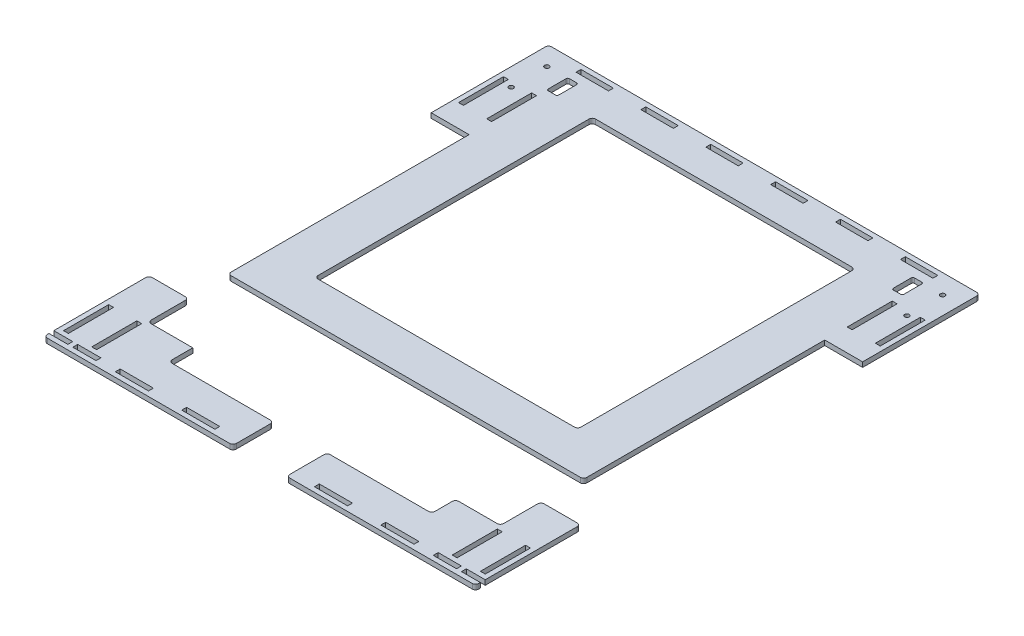
SolidWorks part; units mm, degrees
ref_plane "Front Plane" through (0, 0, 0) normal (0, 0, 1) x (1, 0, 0)
ref_plane "Top Plane" through (0, 0, 0) normal (0, 1, 0) x (1, 0, 0)
ref_plane "Right Plane" through (0, 0, 0) normal (1, 0, 0) x (0, 0, -1)
sketch "Sketch1" plane through (0, 0, 0) normal (0, 1, 0) x (1, 0, 0)
  line L0 (-127, 149.5) -> (-127, 155.5) construction
  line L1 (-133, -155.5) -> (133, -155.5)
  line L2 (-133, -155.5) -> (-133, 155.5)
  line L3 (-133, 155.5) -> (133, 155.5)
  line L4 (133, -155.5) -> (133, 155.5)
  line L5 (-133, -155.5) -> (133, 155.5) construction
  line L6 (-133, 155.5) -> (133, -155.5) construction
  line L7 (-130, -152.5) -> (130, -152.5) construction
  line L8 (-130, -152.5) -> (-130, 152.5) construction
  line L9 (-130, 152.5) -> (130, 152.5) construction
  line L10 (130, -152.5) -> (130, 152.5) construction
  line L11 (-130, -152.5) -> (130, 152.5) construction
  line L12 (-130, 152.5) -> (130, -152.5) construction
  line L13 (-127, -149.5) -> (127, -149.5) construction
  line L14 (-127, -149.5) -> (-127, 149.5) construction
  line L15 (-127, 149.5) -> (127, 149.5) construction
  line L16 (127, -149.5) -> (127, 149.5) construction
  line L17 (-127, -149.5) -> (127, 149.5) construction
  line L18 (-127, 149.5) -> (127, -149.5) construction
  line L19 (-127, 149.5) -> (-133, 149.5) construction
  line L20 (-130, 152.5) -> (-110, 152.5) construction
  line L21 (-110, 149.5) -> (-90, 149.5)
  line L22 (-110, 149.5) -> (-110, 152.5)
  line L23 (-110, 152.5) -> (-90, 152.5)
  line L24 (-90, 149.5) -> (-90, 152.5)
  line L25 (-110, 149.5) -> (-90, 152.5) construction
  line L26 (-110, 152.5) -> (-90, 149.5) construction
  line L27 (-30, 149.5) -> (-10, 149.5)
  line L28 (-30, 149.5) -> (-30, 152.5)
  line L29 (-30, 152.5) -> (-10, 152.5)
  line L30 (-10, 149.5) -> (-10, 152.5)
  line L31 (-30, 149.5) -> (-10, 152.5) construction
  line L32 (-30, 152.5) -> (-10, 149.5) construction
  line L33 (-70, 149.5) -> (-50, 149.5)
  line L34 (-70, 149.5) -> (-70, 152.5)
  line L35 (-70, 152.5) -> (-50, 152.5)
  line L36 (-50, 149.5) -> (-50, 152.5)
  line L37 (-70, 149.5) -> (-50, 152.5) construction
  line L38 (-70, 152.5) -> (-50, 149.5) construction
  line L39 (10, 149.5) -> (30, 149.5)
  line L40 (10, 149.5) -> (10, 152.5)
  line L41 (10, 152.5) -> (30, 152.5)
  line L42 (30, 149.5) -> (30, 152.5)
  line L43 (10, 149.5) -> (30, 152.5) construction
  line L44 (10, 152.5) -> (30, 149.5) construction
  line L45 (50, 149.5) -> (70, 149.5)
  line L46 (50, 149.5) -> (50, 152.5)
  line L47 (50, 152.5) -> (70, 152.5)
  line L48 (70, 149.5) -> (70, 152.5)
  line L49 (50, 149.5) -> (70, 152.5) construction
  line L50 (50, 152.5) -> (70, 149.5) construction
  line L51 (90, 149.5) -> (110, 149.5)
  line L52 (90, 149.5) -> (90, 152.5)
  line L53 (90, 152.5) -> (110, 152.5)
  line L54 (110, 149.5) -> (110, 152.5)
  line L55 (90, 149.5) -> (110, 152.5) construction
  line L56 (90, 152.5) -> (110, 149.5) construction
  line L57 (-90, 152.5) -> (-70, 152.5) construction
  line L58 (-50, 152.5) -> (-30, 152.5) construction
  line L59 (-10, 152.5) -> (10, 152.5) construction
  line L60 (30, 152.5) -> (50, 152.5) construction
  line L61 (70, 152.5) -> (90, 152.5) construction
  line L62 (110, 152.5) -> (130, 152.5) construction
  line L63 (10.2307, -149.5) -> (30.6922, -149.5) construction
  line L64 (-10.2308, -152.5) -> (10.2307, -152.5)
  line L65 (-10.2308, -152.5) -> (-10.2308, -149.5)
  line L66 (-10.2308, -149.5) -> (10.2307, -149.5)
  line L67 (10.2307, -152.5) -> (10.2307, -149.5)
  line L68 (-10.2308, -152.5) -> (10.2307, -149.5) construction
  line L69 (-10.2308, -149.5) -> (10.2307, -152.5) construction
  line L70 (30.6922, -152.5) -> (51.1537, -152.5)
  line L71 (30.6922, -152.5) -> (30.6922, -149.5)
  line L72 (30.6922, -149.5) -> (51.1537, -149.5)
  line L73 (51.1537, -152.5) -> (51.1537, -149.5)
  line L74 (30.6922, -152.5) -> (51.1537, -149.5) construction
  line L75 (30.6922, -149.5) -> (51.1537, -152.5) construction
  line L76 (92.0767, -152.5) -> (71.6152, -152.5)
  line L77 (92.0767, -152.5) -> (92.0767, -149.5)
  line L78 (92.0767, -149.5) -> (71.6152, -149.5)
  line L79 (71.6152, -152.5) -> (71.6152, -149.5)
  line L80 (92.0767, -152.5) -> (71.6152, -149.5) construction
  line L81 (92.0767, -149.5) -> (71.6152, -152.5) construction
  line L82 (-51.1538, -152.5) -> (-30.6923, -152.5)
  line L83 (-51.1538, -152.5) -> (-51.1538, -149.5)
  line L84 (-51.1538, -149.5) -> (-30.6923, -149.5)
  line L85 (-30.6923, -152.5) -> (-30.6923, -149.5)
  line L86 (-51.1538, -152.5) -> (-30.6923, -149.5) construction
  line L87 (-51.1538, -149.5) -> (-30.6923, -152.5) construction
  line L88 (-92.0768, -152.5) -> (-71.6153, -152.5)
  line L89 (-92.0768, -152.5) -> (-92.0768, -149.5)
  line L90 (-92.0768, -149.5) -> (-71.6153, -149.5)
  line L91 (-71.6153, -152.5) -> (-71.6153, -149.5)
  line L92 (-92.0768, -152.5) -> (-71.6153, -149.5) construction
  line L93 (-92.0768, -149.5) -> (-71.6153, -152.5) construction
  line L94 (51.1537, -149.5) -> (71.6152, -149.5) construction
  line L95 (-10.2308, -149.5) -> (-30.6923, -149.5) construction
  line L96 (-51.1538, -149.5) -> (-71.6153, -149.5) construction
  line L97 (-133, 83.1818) -> (-109.65, 83.1818)
  line L98 (133, -152.5) -> (103.975, -152.5)
  line L99 (133, -152.5) -> (133, -149.5)
  line L100 (133, -149.5) -> (103.975, -149.5)
  line L101 (103.975, -152.5) -> (103.975, -149.5)
  line L102 (133, -152.5) -> (103.975, -149.5) construction
  line L103 (133, -149.5) -> (103.975, -152.5) construction
  line L104 (-133, -152.5) -> (-103.975, -152.5)
  line L105 (-133, -152.5) -> (-133, -149.5)
  line L106 (-133, -149.5) -> (-103.975, -149.5)
  line L107 (-103.975, -152.5) -> (-103.975, -149.5)
  line L108 (-133, -152.5) -> (-103.975, -149.5) construction
  line L109 (-133, -149.5) -> (-103.975, -152.5) construction
  line L110 (127, -118.6591) -> (130, -118.6591)
  line L111 (127, -118.6591) -> (127, -146.5)
  line L112 (127, -146.5) -> (130, -146.5)
  line L113 (130, -118.6591) -> (130, -146.5)
  line L114 (127, -118.6591) -> (130, -146.5) construction
  line L115 (127, -146.5) -> (130, -118.6591) construction
  line L120 (-109.65, 83.1818) -> (-109.65, -90.8182)
  line L121 (-109.65, -90.8182) -> (-133, -90.8182)
  line L123 (127, 97.0454) -> (130, 97.0454)
  line L124 (127, 97.0454) -> (127, 124.7727)
  line L125 (127, 124.7727) -> (130, 124.7727)
  line L126 (130, 97.0454) -> (130, 124.7727)
  line L127 (127, 97.0454) -> (130, 124.7727) construction
  line L128 (127, 124.7727) -> (130, 97.0454) construction
  line L134 (133, 83.1818) -> (109.65, 83.1818)
  line L146 (0, -773.499) -> (0, 49226.501) construction
  line L147 (-127, -146.5) -> (-130, -146.5)
  line L148 (-130, -118.6591) -> (-130, -146.5)
  line L149 (-127, -118.6591) -> (-130, -118.6591)
  line L150 (-127, -118.6591) -> (-127, -146.5)
  line L155 (-127, 124.7727) -> (-130, 124.7727)
  line L156 (-130, 97.0454) -> (-130, 124.7727)
  line L157 (-127, 97.0454) -> (-130, 97.0454)
  line L158 (-127, 97.0454) -> (-127, 124.7727)
  line L173 (-127, 110.909) -> (-112.65, 110.909) construction
  line L174 (-81, -130.5) -> (81, -130.5)
  line L175 (-81, -130.5) -> (-81, 130.5)
  line L176 (-81, 130.5) -> (81, 130.5)
  line L177 (81, -130.5) -> (81, 130.5)
  line L178 (-81, -130.5) -> (81, 130.5) construction
  line L179 (-81, 130.5) -> (81, -130.5) construction
  line L184 (109.65, 83.1818) -> (109.65, -90.8182)
  line L185 (109.65, -90.8182) -> (133, -90.8182)
  line L190 (127, -132.5796) -> (112.65, -132.5796) construction
  line L191 (109.65, -146.5) -> (112.65, -146.5)
  line L192 (-112.4444, -152.5) -> (-133, -152.5)
  line L193 (-112.4444, -152.5) -> (-112.4444, -149.5)
  line L194 (-112.4444, -149.5) -> (-133, -149.5)
  line L195 (-133, -152.5) -> (-133, -149.5)
  line L196 (-112.4444, -152.5) -> (-133, -149.5) construction
  line L197 (-112.4444, -149.5) -> (-133, -152.5) construction
  line L198 (112.4444, -152.5) -> (133, -152.5)
  line L199 (112.4444, -152.5) -> (112.4444, -149.5)
  line L200 (112.4444, -149.5) -> (133, -149.5)
  line L201 (133, -152.5) -> (133, -149.5)
  line L202 (112.4444, -152.5) -> (133, -149.5) construction
  line L203 (112.4444, -149.5) -> (133, -152.5) construction
  line L204 (109.65, 97.0454) -> (112.65, 97.0454)
  line L205 (109.65, 97.0454) -> (109.65, 124.7727)
  line L206 (109.65, 124.7727) -> (112.65, 124.7727)
  line L207 (112.65, 97.0454) -> (112.65, 124.7727)
  line L208 (109.65, 97.0454) -> (112.65, 124.7727) construction
  line L209 (109.65, 124.7727) -> (112.65, 97.0454) construction
  line L210 (-109.65, 97.0454) -> (-112.65, 97.0454)
  line L211 (-109.65, 97.0454) -> (-109.65, 124.7727)
  line L212 (-109.65, 124.7727) -> (-112.65, 124.7727)
  line L213 (-112.65, 97.0454) -> (-112.65, 124.7727)
  line L214 (-109.65, 97.0454) -> (-112.65, 124.7727) construction
  line L215 (-109.65, 124.7727) -> (-112.65, 97.0454) construction
  line L216 (127, 110.909) -> (112.65, 110.909) construction
  line L217 (109.65, -146.5) -> (109.65, -118.6591)
  line L218 (109.65, -118.6591) -> (112.65, -118.6591)
  line L219 (112.65, -146.5) -> (112.65, -118.6591)
  line L220 (109.65, -146.5) -> (112.65, -118.6591) construction
  line L221 (109.65, -118.6591) -> (112.65, -146.5) construction
  line L222 (-109.65, -146.5) -> (-112.65, -146.5)
  line L223 (-109.65, -146.5) -> (-109.65, -118.6591)
  line L224 (-109.65, -118.6591) -> (-112.65, -118.6591)
  line L225 (-112.65, -146.5) -> (-112.65, -118.6591)
  line L226 (-109.65, -146.5) -> (-112.65, -118.6591) construction
  line L227 (-109.65, -118.6591) -> (-112.65, -146.5) construction
  line L228 (-112.65, -132.5796) -> (-127, -132.5796) construction
  point P0 (0, 0)
  point P6 (0, 0)
  point P11 (0, 0)
  point P16 (-100, 151)
  point P19 (-127, 152.5)
  point P21 (-130, 149.5)
  point P25 (-20, 151)
  point P30 (-60, 151)
  point P35 (20, 151)
  point P40 (60, 151)
  point P45 (100, 151)
  point P50 (128.5, -132.5796)
  point P51 (0, -151)
  point P56 (40.923, -151)
  point P61 (81.846, -151)
  point P66 (-40.923, -151)
  point P71 (-81.846, -151)
  point P76 (-118.4875, -151)
  point P81 (128.5, 110.909)
  point P85 (111.15, -132.5796)
  point P88 (118.4875, -151)
  point P108 (-111.15, -132.5796)
  point P114 (122.7222, -151)
  point P135 (-122.7222, -151)
  point P136 (111.15, 110.909)
  point P145 (0, 0)
  point P154 (-111.15, 110.909)
  dimension "D1" = 266
  dimension "D2" = 311
  dimension "D3" = 6
  dimension "D4" = 20.4615
  dimension "D5" = 29.025
  dimension "D6" = 3
  dimension "D7" = 27.8409
  dimension "D8" = 27.7273
  dimension "D9" = 24.7273
  dimension "D10" = 13.8636
  dimension "D11" = 174
  dimension "D12" = 14.35
  dimension "D15" = 20.5556
  dimension "D16" = 14.35
  dimension "D17" = 25
  dimension "D18" = 52
extrude "Boss-Extrude1" add sketch "Sketch1" along normal blind 3
sketch "Sketch4" plane through (0, 0, 0) normal (0, -1, 0) x (1, 0, 0)
  line L0 (-81, 130.5) -> (-81, -130.5) construction
  line L1 (-81, 40.5) -> (81, 40.5)
  line L2 (-81, 40.5) -> (-81, 65.5)
  line L3 (-81, 65.5) -> (81, 65.5)
  line L4 (81, 40.5) -> (81, 65.5)
  line L5 (-81, 40.5) -> (81, 65.5) construction
  line L6 (-81, 65.5) -> (81, 40.5) construction
  line L7 (81, 130.5) -> (81, -130.5) construction
  line L8 (-133, 155.5) -> (133, 155.5) construction
  point P0 (0, 53)
  dimension "D1" = 25
  dimension "D2" = 90
extrude "Boss-Extrude2" add sketch "Sketch4" against normal up to surface (3 mm away) up to face at (111.15, 3, 132.5796)
sketch "Sketch3" plane through (0, 3, 0) normal (0, 1, 0) x (1, 0, 0)
  line L0 (-81, -130.5) -> (81, -130.5) construction
  line L1 (-16.5, -155.5) -> (16.5, -155.5)
  line L2 (-16.5, -155.5) -> (-16.5, -130.5)
  line L3 (-16.5, -130.5) -> (16.5, -130.5)
  line L4 (16.5, -155.5) -> (16.5, -130.5)
  line L5 (-16.5, -155.5) -> (16.5, -130.5) construction
  line L6 (-16.5, -130.5) -> (16.5, -155.5) construction
  line L7 (-133, -155.5) -> (133, -155.5) construction
  line L8 (-109.65, -146.5) -> (-109.65, -118.6591) construction
  line L9 (109.65, -90.8182) -> (81, -90.8182)
  line L10 (109.65, -90.8182) -> (109.65, -65.5)
  line L11 (109.65, -65.5) -> (81, -65.5)
  line L12 (81, -90.8182) -> (81, -65.5)
  line L13 (109.65, -90.8182) -> (81, -65.5) construction
  line L14 (109.65, -65.5) -> (81, -90.8182) construction
  line L15 (-109.65, -90.8182) -> (-81, -90.8182)
  line L16 (-109.65, -90.8182) -> (-109.65, -65.5)
  line L17 (-109.65, -65.5) -> (-81, -65.5)
  line L18 (-81, -90.8182) -> (-81, -65.5)
  line L19 (-109.65, -90.8182) -> (-81, -65.5) construction
  line L20 (-109.65, -65.5) -> (-81, -90.8182) construction
  line L21 (108.65, -115.8182) -> (81, -115.8182)
  line L22 (108.65, -115.8182) -> (108.65, -90.8182)
  line L23 (108.65, -90.8182) -> (81, -90.8182)
  line L24 (81, -115.8182) -> (81, -90.8182)
  line L25 (108.65, -115.8182) -> (81, -90.8182) construction
  line L26 (108.65, -90.8182) -> (81, -115.8182) construction
  line L27 (-108.65, -115.8182) -> (-81, -115.8182)
  line L28 (-108.65, -115.8182) -> (-108.65, -90.8182)
  line L29 (-108.65, -90.8182) -> (-81, -90.8182)
  line L30 (-81, -115.8182) -> (-81, -90.8182)
  line L31 (-108.65, -115.8182) -> (-81, -90.8182) construction
  line L32 (-108.65, -90.8182) -> (-81, -115.8182) construction
  line L34 (-1.65, -60.5) -> (-1.65, -55.5)
  line L35 (1.65, -60.5) -> (1.65, -55.5)
  line L36 (81, -65.5) -> (-81, -65.5) construction
  arc A1 (-1.65, -60.5) -> (1.65, -60.5) centre (0, -60.5) ccw
  arc A2 (-1.65, -55.5) -> (1.65, -55.5) centre (0, -55.5) cw
  point P0 (0, -143)
  point P7 (95.325, -78.1591)
  point P16 (-95.325, -78.1591)
  point P22 (-94.825, -103.3182)
  point P27 (94.825, -103.3182)
  dimension "D4" = 1.65
  dimension "D5" = 5
  dimension "D1" = 33
  dimension "D2" = 1
  dimension "D3" = 25
  dimension "D6" = 5
extrude "Cut-Extrude2" cut sketch "Sketch3" against normal through all both and the other way through all contours L15 L18 L17 L16 | L27 L30 L15 L28 | L1 L4 L3 L2 | L24 L21 L22 L9 | L12 L9 L10 L11
fillet "Fillet1" radius 2 8 edges at (133, 1.5, -155.5) (-133, 1.5, -155.5) (-81, 1.5, -130.5) (81, 1.5, -130.5) (81, 1.5, 40.5) (-81, 1.5, 40.5) (-109.65, 1.5, 65.5) (109.65, 1.5, 65.5)
fillet "Fillet2" radius 2 7 edges at (-81, 1.5, 130.5) (-16.5, 1.5, 130.5) (-16.5, 1.5, 155.5) (-133, 1.5, 155.5) (-133, 1.5, 90.8182) (-108.65, 1.5, 90.8182) (-108.65, 1.5, 115.8182)
fillet "Fillet3" radius 2 8 edges at (133, 1.5, 90.8182) (133, 1.5, 155.5) (81, 1.5, 130.5) (16.5, 1.5, 130.5) (16.5, 1.5, 155.5) (108.65, 1.5, 90.8182) (108.65, 1.5, 115.8182) (81, 1.5, 115.8182)
sketch "Sketch5" plane through (0, 0, 0) normal (0, 1, 0) x (1, 0, 0)
  line L0 (-133, -149.5) -> (-103.975, -149.5) construction
  line L1 (-121.325, -152.5) -> (-118.325, -152.5)
  line L2 (-121.325, -152.5) -> (-121.325, -149.5)
  line L3 (-121.325, -149.5) -> (-118.325, -149.5)
  line L4 (-118.325, -152.5) -> (-118.325, -149.5)
  line L5 (-121.325, -152.5) -> (-118.325, -149.5) construction
  line L6 (-121.325, -149.5) -> (-118.325, -152.5) construction
  line L7 (103.975, -149.5) -> (133, -149.5) construction
  line L8 (118.325, -152.5) -> (121.325, -152.5)
  line L9 (118.325, -152.5) -> (118.325, -149.5)
  line L10 (118.325, -149.5) -> (121.325, -149.5)
  line L11 (121.325, -152.5) -> (121.325, -149.5)
  line L12 (118.325, -152.5) -> (121.325, -149.5) construction
  line L13 (118.325, -149.5) -> (121.325, -152.5) construction
  line L14 (-103.975, -152.5) -> (-133, -152.5) construction
  line L15 (-127, -146.5) -> (-112.65, -146.5) construction
  line L16 (112.65, -146.5) -> (127, -146.5) construction
  line L17 (112.65, -146.5) -> (112.65, -118.6591) construction
  point P0 (-119.825, -151)
  point P7 (119.825, -151)
  point P25 (119.825, -146.5)
  point P26 (-119.825, -146.5)
extrude "Boss-Extrude3" add sketch "Sketch5" along normal up to surface (3 mm away) up to face at (-111.15, 3, -110.909)
sketch "Sketch6" plane through (0, 3, 0) normal (0, 1, 0) x (1, 0, 0)
  line L0 (-131, 155.5) -> (131, 155.5) construction
  line L1 (-133, 83.1818) -> (-133, 153.5) construction
  line L2 (0, -1.65) -> (0, 1.65) construction
  line L3 (-109.65, 97.0454) -> (-109.65, 124.7727) construction
  line L4 (-104.15, 131) -> (-108.65, 131)
  line L5 (-103.15, 132) -> (-103.15, 143)
  line L6 (-104.15, 144) -> (-108.65, 144)
  line L7 (-109.65, 132) -> (-109.65, 143)
  line L8 (-103.15, 131) -> (-109.65, 144) construction
  line L9 (-103.15, 144) -> (-109.65, 131) construction
  line L11 (104.15, 144) -> (108.65, 144)
  line L12 (109.65, 132) -> (109.65, 143)
  line L13 (104.15, 131) -> (108.65, 131)
  line L14 (103.15, 132) -> (103.15, 143)
  circle A0 centre (-122, 143.5) radius 1.4
  circle A1 centre (-122, 121.5) radius 1.4
  circle A2 centre (122, 121.5) radius 1.4
  circle A3 centre (122, 143.5) radius 1.4
  arc A4 (-104.15, 131) -> (-103.15, 132) centre (-104.15, 132) ccw
  arc A5 (-108.65, 131) -> (-109.65, 132) centre (-108.65, 132) cw
  arc A6 (-108.65, 144) -> (-109.65, 143) centre (-108.65, 143) ccw
  arc A7 (-103.15, 143) -> (-104.15, 144) centre (-104.15, 143) ccw
  arc A8 (108.65, 144) -> (109.65, 143) centre (108.65, 143) cw
  arc A9 (108.65, 131) -> (109.65, 132) centre (108.65, 132) ccw
  arc A10 (104.15, 131) -> (103.15, 132) centre (104.15, 132) cw
  arc A11 (103.15, 143) -> (104.15, 144) centre (104.15, 143) cw
  point P15 (-106.4, 137.5)
  dimension "D1" = 12
  dimension "D2" = 34
  dimension "D3" = 6.5
  dimension "D4" = 11
  dimension "D5" = 2.8
  dimension "D9" = 1
  dimension "D7" = 13
  dimension "D8" = 11.5
extrude "Cut-Extrude3" cut sketch "Sketch6" against normal through all both and the other way through all
